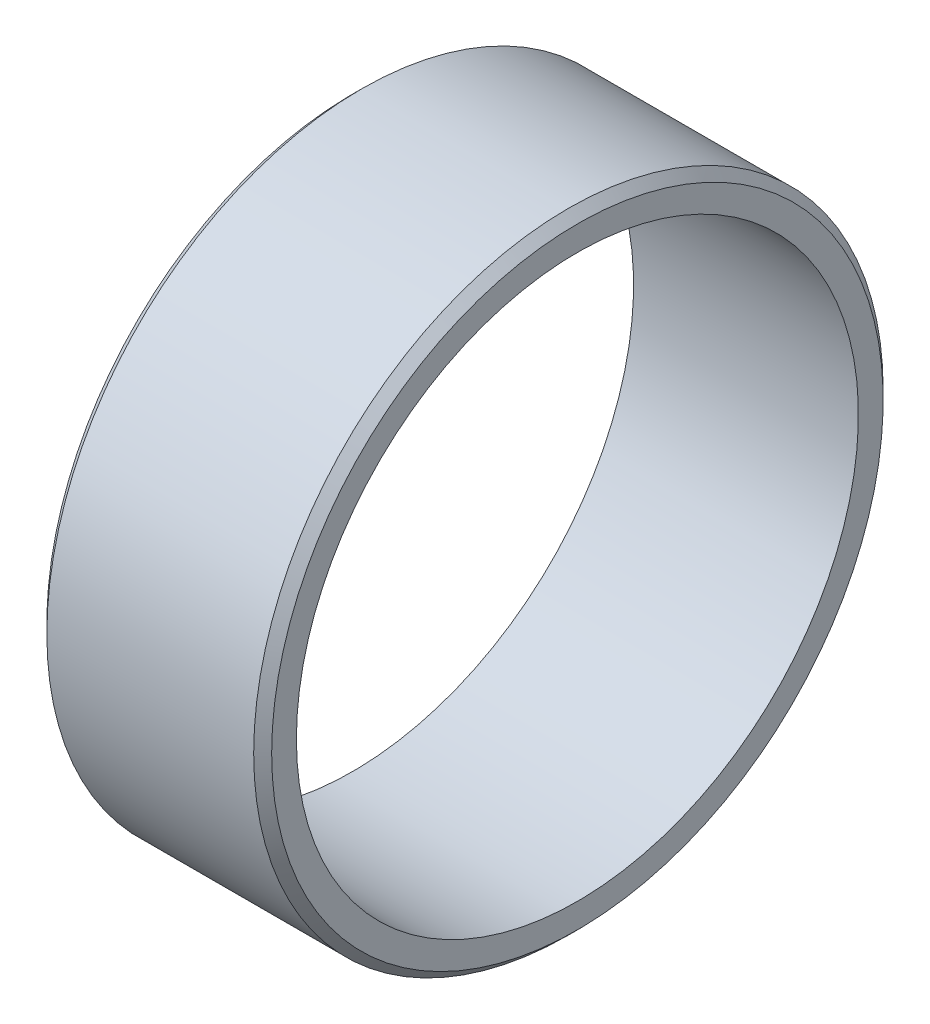
SolidWorks part; units mm, degrees
material "Plain Carbon Steel"
ref_plane "Front Plane" through (0, 0, 0) normal (0, 0, 1) x (1, 0, 0)
ref_plane "Top Plane" through (0, 0, 0) normal (0, 1, 0) x (1, 0, 0)
ref_plane "Right Plane" through (0, 0, 0) normal (1, 0, 0) x (0, 0, -1)
sketch "Sketch1" plane through (0, 0, 0) normal (0, 0, 1) x (1, 0, 0)
  line L0 (0, 0) -> (18.6017, 0) construction
  line L2 (5, 12.5) -> (-5, 12.5)
  line L3 (5, 12.5) -> (5, 14)
  line L4 (5, 14) -> (-5, 14)
  line L5 (-5, 12.5) -> (-5, 14)
  line L6 (5, 12.5) -> (-5, 14) construction
  line L7 (5, 14) -> (-5, 12.5) construction
  point P3 (0, 13.25)
  dimension "D1" = 10
  dimension "D2" = 25
  dimension "D3" = 28
revolve "Revolve1" add sketch "Sketch1" angle 360 about L0
chamfer "Chamfer1" distance 0.4 angle 45 2 edges at (-5, 0, 14) (5, 0, 14)
